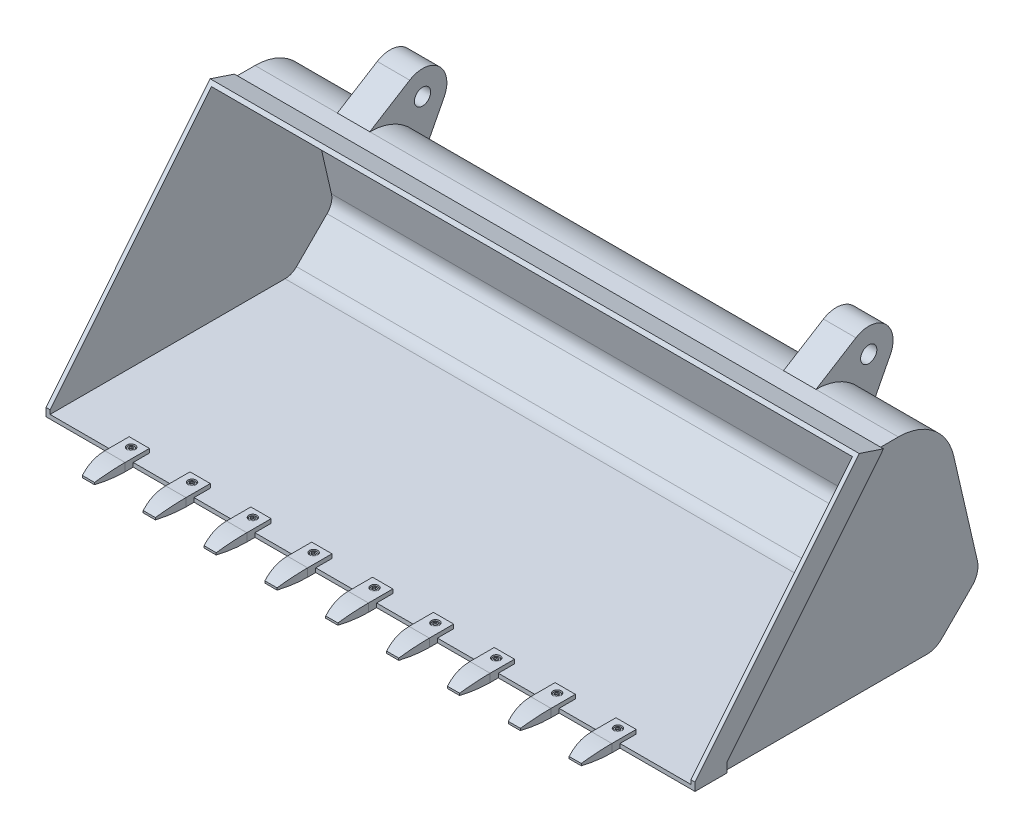
SolidWorks part; units mm, degrees
ref_plane "Front Plane" through (0, 0, 0) normal (0, 0, 1) x (1, 0, 0)
ref_plane "Top Plane" through (0, 0, 0) normal (0, 1, 0) x (1, 0, 0)
ref_plane "Right Plane" through (0, 0, 0) normal (1, 0, 0) x (0, 0, -1)
sketch "Sketch1" plane through (0, 0, 0) normal (1, 0, 0) x (0, 0, -1)
  line L0 (-289.6447, 0) -> (289.6447, 0)
  line L1 (325, 14.6447) -> (400.3591, 90.0038)
  line L2 (413.7223, 136.6067) -> (355.0272, 390.8427)
  line L3 (218.6154, 499.3496) -> (174.9765, 499.3496)
  line L4 (174.9765, 499.3496) -> (114.9765, 519.3496)
  line L5 (114.9765, 519.3496) -> (-289.6447, 20)
  line L6 (-289.6447, 20) -> (-289.6447, 0)
  arc A0 (355.0272, 390.8427) -> (218.6154, 499.3496) centre (218.6154, 359.3496) ccw
  arc A1 (325, 14.6447) -> (289.6447, 0) centre (289.6447, 50) cw
  arc A2 (413.7223, 136.6067) -> (400.3591, 90.0038) centre (365.0038, 125.3591) cw
  point P12 (329.9765, 499.3496)
  point P15 (310.3553, 0)
  point P18 (419.9569, 109.6016)
  dimension "D10" = 140
  dimension "D11" = 50
  dimension "D1" = 600
  dimension "D2" = 155
  dimension "D3" = 135
  dimension "D4" = 122
  dimension "D5" = 400
  dimension "D6" = 155
  dimension "D7" = 20
  dimension "D8" = 60
  dimension "D9" = 20
extrude "Boss-Extrude1" add sketch "Sketch1" along normal mid plane 1600
shell "Shell1" thickness 10
sketch "Sketch4" plane through (0, 0, 289.6447) normal (0, 0, 1) x (1, 0, 0)
  line L0 (-790, 21.7157) -> (-790, 97.0748) construction
  line L1 (790, 10) -> (-790, 10)
  line L2 (790, 10) -> (790, 44)
  line L3 (790, 44) -> (-790, 44)
  line L4 (-790, 10) -> (-790, 44)
  line L5 (800, 0) -> (-800, 0) construction
  dimension "D1" = 10
  dimension "D2" = 34
extrude "Cut-Extrude2" cut sketch "Sketch4" against normal up to next
sketch "Sketch5" plane through (800, 0, 0) normal (1, 0, 0) x (0, 0, -1)
  line L0 (325, 14.6447) -> (400.3591, 90.0038) construction
  line L1 (413.7223, 136.6067) -> (355.0272, 390.8427) construction
  line L2 (218.6154, 499.3496) -> (174.9765, 499.3496) construction
  line L3 (325, 14.6447) -> (400.3591, 90.0038)
  line L4 (413.7223, 136.6067) -> (355.0272, 390.8427)
  line L5 (218.6154, 499.3496) -> (174.9765, 499.3496)
  line L6 (174.9765, 499.3496) -> (-210.3553, 23.8053)
  line L7 (-210.3553, 23.8053) -> (-210.3553, 0)
  line L8 (-289.6447, 0) -> (289.6447, 0) construction
  line L9 (-210.3553, 0) -> (289.6447, 0)
  line L10 (114.9765, 519.3496) -> (-289.6447, 20) construction
  arc A0 (289.6447, 0) -> (325, 14.6447) centre (289.6447, 50) ccw construction
  arc A1 (400.3591, 90.0038) -> (413.7223, 136.6067) centre (365.0038, 125.3591) ccw construction
  arc A2 (355.0272, 390.8427) -> (218.6154, 499.3496) centre (218.6154, 359.3496) ccw construction
  arc A3 (289.6447, 0) -> (325, 14.6447) centre (289.6447, 50) ccw
  arc A4 (400.3591, 90.0038) -> (413.7223, 136.6067) centre (365.0038, 125.3591) ccw
  arc A5 (355.0272, 390.8427) -> (218.6154, 499.3496) centre (218.6154, 359.3496) ccw
  dimension "D1" = 500
extrude "Cut-Extrude3" cut sketch "Sketch5" against normal blind 7
ref_plane "Plane1" through (590, 0, 0) normal (1, 0, 0) x (0, 0, -1)
sketch "Sketch6" plane through (590, 0, 0) normal (1, 0, 0) x (0, 0, -1)
  line L0 (218.6154, 499.3496) -> (317.0004, 560.3446)
  line L1 (401.9461, 481.857) -> (355.0272, 390.8427)
  circle A0 centre (348.6154, 509.3496) radius 20
  arc A1 (355.0272, 390.8427) -> (218.6154, 499.3496) centre (218.6154, 359.3496) ccw construction
  arc A2 (317.0004, 560.3446) -> (401.9461, 481.857) centre (348.6154, 509.3496) cw
  arc A3 (355.0272, 390.8427) -> (218.6154, 499.3496) centre (218.6154, 359.3496) ccw
  dimension "D3" = 40
  dimension "D4" = 60
  dimension "D1" = 150
  dimension "D2" = 130
extrude "Boss-Extrude2" add sketch "Sketch6" against normal blind 80
mirror "Mirror1" about plane through (0, 0, 0) normal (1, 0, 0) of "Boss-Extrude2", "Cut-Extrude3"
sketch "Sketch7" plane through (590, 0, 0) normal (1, 0, 0) x (0, 0, -1)
  line L0 (-249.6447, 20) -> (-249.6447, 10)
  line L1 (-289.6447, 10) -> (289.6447, 10) construction
  line L2 (-249.6447, 10) -> (-289.6447, 10)
  line L3 (-289.6447, 10) -> (-289.6447, 0)
  line L5 (-289.6447, 0) -> (-375.0281, 0)
  line L6 (-375.0281, 0) -> (-375.0281, 5)
  line L7 (-249.6447, 20) -> (-309.6447, 20)
  arc A0 (-309.6447, 20) -> (-375.0281, 5) centre (-309.6447, -130) ccw
  dimension "D5" = 150
  dimension "D1" = 10
  dimension "D2" = 40
  dimension "D3" = 60
  dimension "D4" = 5
  dimension "D6" = 10
extrude "Boss-Extrude3" add sketch "Sketch7" along normal mid plane 50 separate body
sketch "Sketch8" plane through (0, 20, 0) normal (0, 1, 0) x (1, 0, 0)
  line L2 (615, -249.6447) -> (565, -289.6447) construction
  circle A0 centre (590, -269.6447) radius 6
  point P3 (590, -269.6447)
  dimension "D1" = 12
extrude "Cut-Extrude4" cut sketch "Sketch8" against normal through all
sketch "Sketch9" plane through (0, 20, 0) normal (0, 1, 0) x (1, 0, 0)
  circle A0 centre (590, -269.6447) radius 10
  dimension "D1" = 20
extrude "Cut-Extrude5" cut sketch "Sketch9" against normal blind 10
sketch "Sketch10" plane through (0, 10, 0) normal (0, 1, 0) x (1, 0, 0)
  circle A0 centre (590, -269.6447) radius 8.5
  dimension "D1" = 17
extrude "Boss-Extrude4" add sketch "Sketch10" along normal blind 8 separate body
fillet "Fillet1" radius 1 1 edges at (590, 18, 278.1447)
sketch "Sketch11" plane through (0, 10, 0) normal (0, 1, 0) x (1, 0, 0)
  circle A0 centre (590, -269.6447) radius 6
  dimension "D1" = 12
extrude "Boss-Extrude5" add sketch "Sketch11" against normal blind 8 separate body
sketch "Sketch12" plane through (0, 18, 0) normal (0, 1, 0) x (1, 0, 0)
  line L1 (592.75, -264.8815) -> (587.25, -264.8815)
  line L2 (587.25, -264.8815) -> (584.5, -269.6447)
  line L3 (584.5, -269.6447) -> (587.25, -274.4078)
  line L4 (587.25, -274.4078) -> (592.75, -274.4078)
  line L5 (592.75, -274.4078) -> (595.5, -269.6447)
  line L6 (595.5, -269.6447) -> (592.75, -264.8815)
  circle A0 centre (590, -269.6447) radius 4.7631 construction
  point P1 (590, -264.8815)
  dimension "D1" = 5.5
extrude "Cut-Extrude6" cut sketch "Sketch12" against normal blind 4
sketch "Sketch13" plane through (0, 0, 0) normal (0, -1, 0) x (1, 0, 0)
  line L0 (615, 309.6447) -> (636.0744, 309.6447)
  line L1 (636.0744, 309.6447) -> (636.0744, 389.0996)
  line L2 (636.0744, 389.0996) -> (538.9549, 389.0996)
  line L3 (538.9549, 389.0996) -> (538.9549, 309.6447)
  line L4 (538.9549, 309.6447) -> (565, 309.6447)
  line L5 (615, 375.0281) -> (565, 375.0281) construction
  line L6 (590, 375.0281) -> (590, 294.2652) construction
  line L7 (575, 375.0281) -> (605, 375.0281)
  arc A0 (565, 309.6447) -> (575, 375.0281) centre (783.75, 309.6447) cw
  arc A1 (615, 309.6447) -> (605, 375.0281) centre (396.25, 309.6447) ccw
  dimension "D1" = 30
extrude "Cut-Extrude8" cut sketch "Sketch13" against normal through all
pattern_linear "LPattern3" count 9 spacing 150 along (-1, 0, 0) of bodies 113 139
